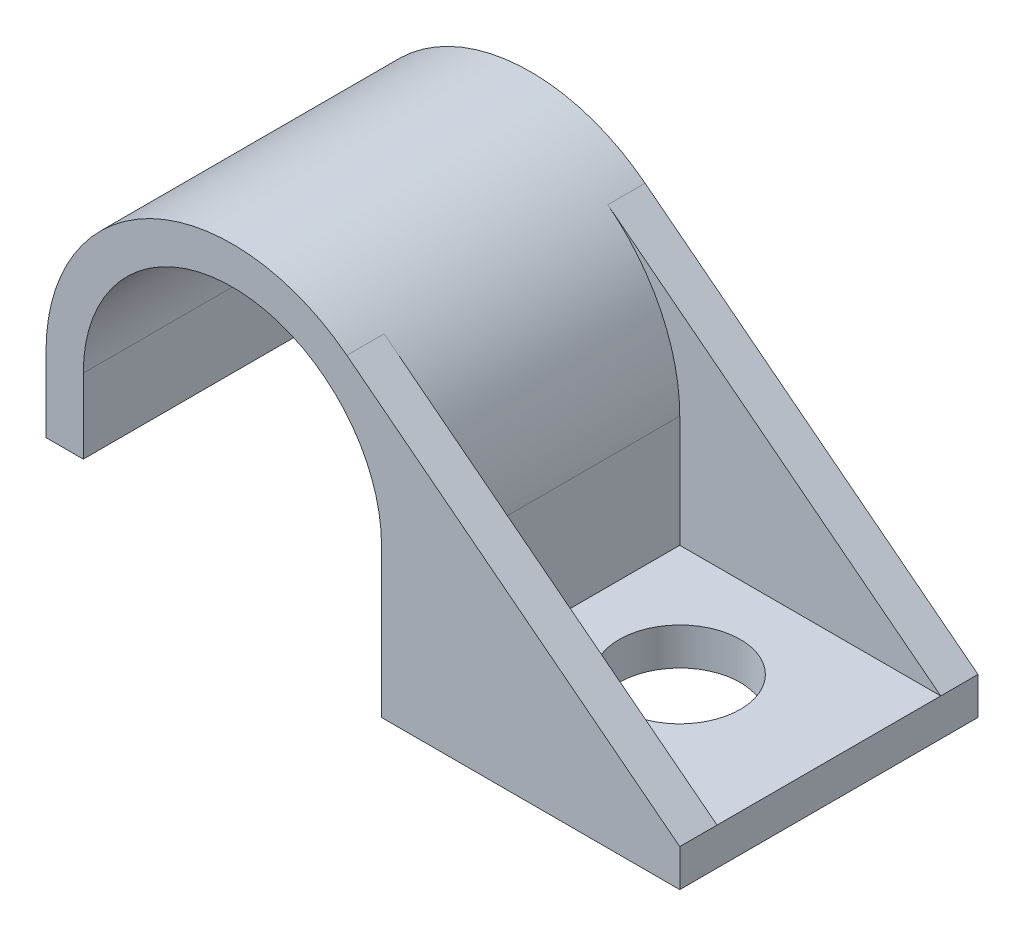
SolidWorks part; units mm, degrees
material "PVC 0.007 Plasticized"
ref_plane "Front" through (0, 0, 0) normal (0, 0, 1) x (1, 0, 0)
ref_plane "Top" through (0, 0, 0) normal (0, 1, 0) x (1, 0, 0)
ref_plane "Right" through (0, 0, 0) normal (1, 0, 0) x (0, 0, -1)
sketch "Sketch1" plane through (0, 0, 0) normal (0, 0, 1) x (1, 0, 0)
  line L11 (0, 14.2875) -> (0, 21.0796) construction
  line L12 (7.9375, 1.5875) -> (7.9375, 10.2318) construction
  line L13 (19.05, 1.5875) -> (7.9375, 1.5875) construction
  line L14 (-7.9375, 3.175) -> (-7.9375, 6.35)
  line L15 (-6.35, 3.175) -> (-7.9375, 3.175)
  line L16 (19.05, 1.5875) -> (4.8736, 12.6152)
  line L17 (19.05, 0) -> (19.05, 1.5875)
  line L18 (6.35, 0) -> (19.05, 0)
  line L19 (6.35, 6.35) -> (6.35, 0)
  line L20 (-6.35, 6.35) -> (-6.35, 3.175)
  arc A0 (6.35, 6.35) -> (-6.35, 6.35) centre (0, 6.35) ccw
  arc A5 (-7.9375, 6.35) -> (4.8736, 12.6152) centre (0, 6.35) cw
  point P2 (1.5181, 2.0516)
  point P13 (4.1275, 1.5875)
  point P41 (12.7, 0)
  dimension "D1" = 3.175
extrude "Boss-Extrude1" add sketch "Sketch1" along normal mid plane 12.7
sketch "Sketch4" plane through (0, 0, 0) normal (0, 1, 0) x (1, 0, 0)
  line L1 (7.9375, 4.7625) -> (19.05, 4.7625)
  line L2 (7.9375, 4.7625) -> (7.9375, -4.7625)
  line L3 (7.9375, -4.7625) -> (19.05, -4.7625)
  line L4 (19.05, 4.7625) -> (19.05, -4.7625)
  line L7 (19.05, -6.35) -> (19.05, 6.35) construction
  line L8 (6.35, 6.35) -> (19.05, 6.35) construction
  point P6 (19.05, 0)
  dimension "D1" = 1.5875
extrude "Cut-Extrude3" cut sketch "Sketch4" along normal through all from vertex at 1.5875 starting at point (19.05, 1.5875, 0)
sketch "Sketch5" plane through (0, 0, 0) normal (0, 0, 1) x (1, 0, 0)
  line L0 (7.9375, 1.5875) -> (7.9375, 10.2318) construction
  line L1 (7.9375, 6.35) -> (7.9375, 10.2318)
  line L3 (19.05, 1.5875) -> (4.8736, 12.6152) construction
  line L4 (7.9375, 10.2318) -> (4.8736, 12.6152)
  arc A1 (4.8736, 12.6152) -> (-7.9375, 6.35) centre (0, 6.35) ccw construction
  arc A2 (7.9375, 6.35) -> (4.8736, 12.6152) centre (0, 6.35) ccw
extrude "Cut-Extrude4" cut sketch "Sketch5" along normal up to surface and the other way up to surface up to face at (11.6417, 4.4689, 4.7625) other way up to face at (11.6417, 4.4689, -4.7625)
sketch "Sketch3" plane through (0, 0, 0) normal (0, 1, 0) x (1, 0, 0)
  circle A0 centre (12.7, 0) radius 2.5797
  dimension "Mounting Hole Dia" = 5.1594
extrude "Cut-Extrude2" cut sketch "Sketch3" along normal blind 2.54
sketch "Sketch7" plane through (0, 0, 0) normal (0, 1, 0) x (1, 0, 0)
  line L0 (0, 6.985) -> (0, -6.985)
  line L2 (4.8736, 6.35) -> (-7.9375, 6.35) construction
  dimension "D1" = 0.635
equation "\"D1@Sketch1\" = \"ID@Sketch1\" * .25"
equation "\"D1@Sketch4\" = \"Thickness@Sketch1\""
